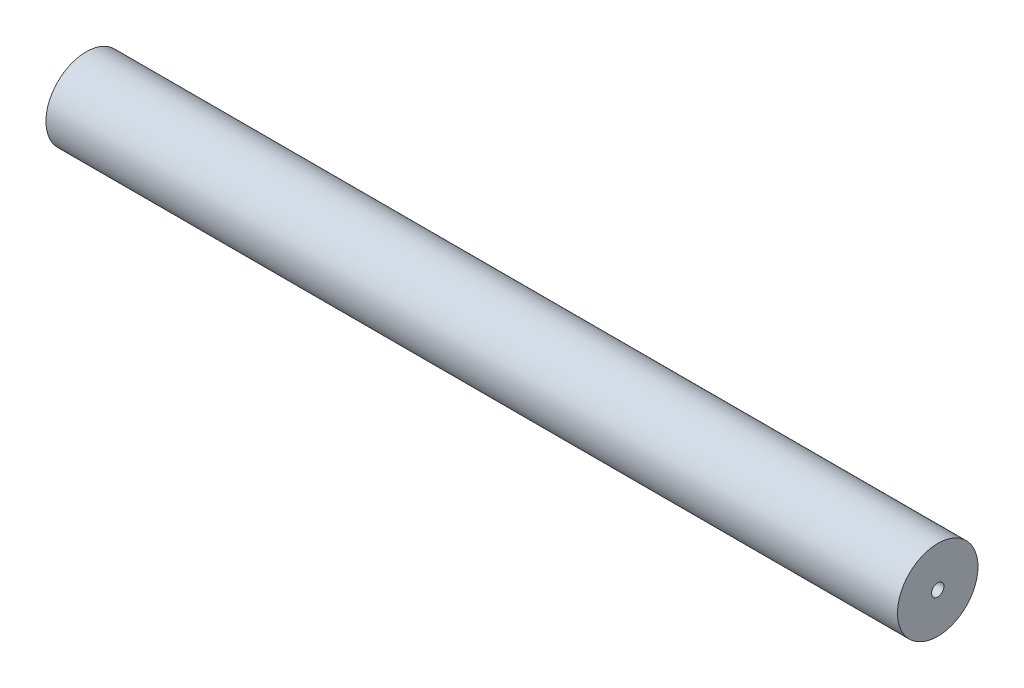
SolidWorks part; units mm, degrees
material "AISI 316 Annealed Stainless Steel Bar (SS)"
ref_plane "Front Plane" through (0, 0, 0) normal (0, 0, 1) x (1, 0, 0)
ref_plane "Top Plane" through (0, 0, 0) normal (0, 1, 0) x (1, 0, 0)
ref_plane "Right Plane" through (0, 0, 0) normal (1, 0, 0) x (0, 0, -1)
sketch "Sketch1" plane through (0, 0, 0) normal (0, 0, 1) x (1, 0, 0)
  line L1 (11, 0.5) -> (11, 3.25)
  line L2 (11, 3.25) -> (-56.55, 3.25) construction
  line L3 (10, 0.5) -> (11, 0.5)
  line L4 (10, 0.5) -> (10, 2.25)
  line L5 (10, 2.25) -> (-57.75, 2.25)
  line L7 (-57.75, 5.25) -> (-56.55, 5.25) construction
  line L8 (-56.55, 5.25) -> (-56.55, 3.25) construction
  line L9 (-57.75, 2.25) -> (-57.75, 5.25) construction
  line L10 (11, 3.25) -> (-57.75, 3.25)
  line L11 (-57.75, 3.25) -> (-57.75, 2.25)
  dimension "D1" = 3.25
  dimension "D2" = 2.75
  dimension "D3" = 1
  dimension "D4" = 1
  dimension "D5" = 3
  dimension "D6" = 10
  dimension "D7" = 1.2
  dimension "D8" = 68.75
ref_axis "Axis1" through (13.5, 0, 0) along (-1, 0, 0)
revolve "Revolve1" add sketch "Sketch1" angle 360 about axis through (13.5, 0, 0) along (-1, 0, 0)
